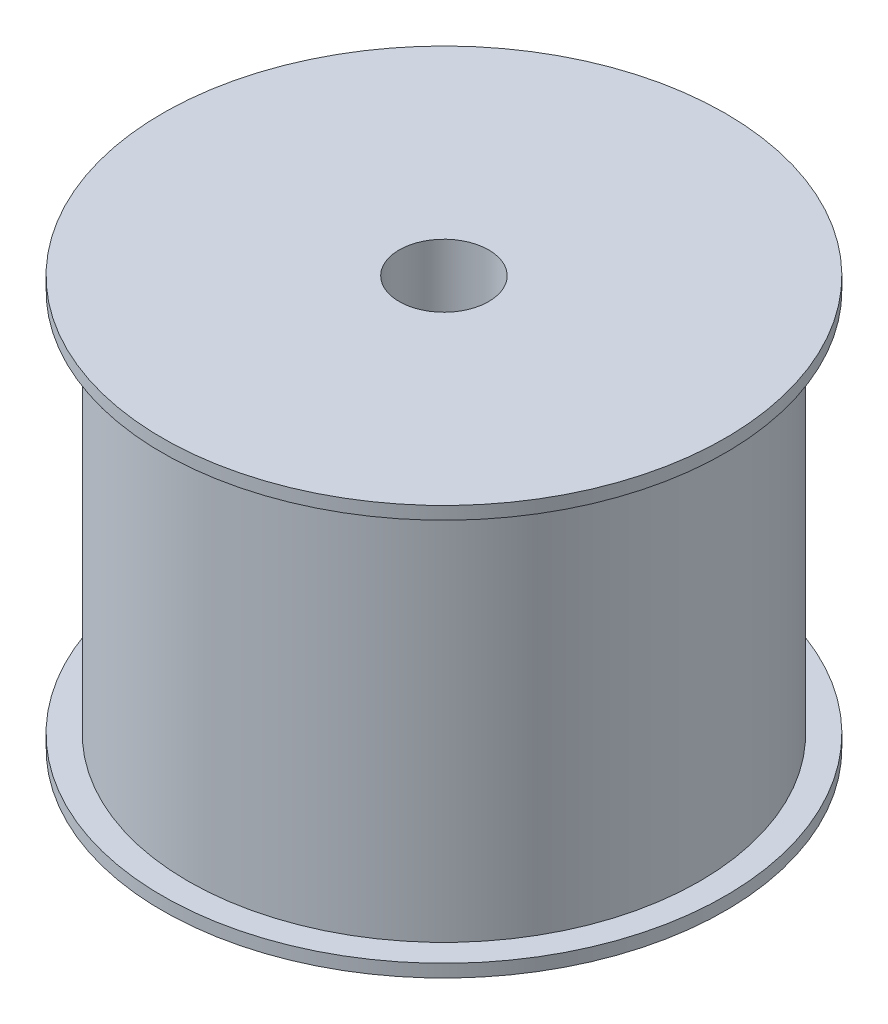
SolidWorks part; units mm, degrees
ref_plane "Front Plane" through (0, 0, 0) normal (0, 0, 1) x (1, 0, 0)
ref_plane "Top Plane" through (0, 0, 0) normal (0, 1, 0) x (1, 0, 0)
ref_plane "Right Plane" through (0, 0, 0) normal (1, 0, 0) x (0, 0, -1)
sketch "Sketch2" plane through (0, 0, 0) normal (0, 0, 1) x (1, 0, 0)
  line L0 (0, 0) -> (0, 17.687) construction
  line L1 (1.75, 9.0208) -> (11, 9.0208)
  line L2 (11, 9.0208) -> (11, 8.5208)
  line L3 (11, 8.5208) -> (10, 8.5208)
  line L4 (10, 8.5208) -> (10, -6.4792)
  line L5 (10, -6.4792) -> (11, -6.4792)
  line L6 (11, -6.4792) -> (11, -6.9792)
  line L7 (11, -6.9792) -> (2.75, -6.9792)
  line L9 (2.75, -6.9792) -> (2.75, 6.5208)
  line L10 (2.75, 6.5208) -> (1.75, 6.5208)
  line L12 (1.75, 6.5208) -> (1.75, 9.0208)
  dimension "D1" = 0.5
  dimension "D2" = 1
  dimension "D3" = 15
  dimension "D4" = 5.5
  dimension "D5" = 3.5
  dimension "D6" = 2.5
  dimension "D7" = 20
revolve "Revolve1" add sketch "Sketch2" angle 360 about L0
